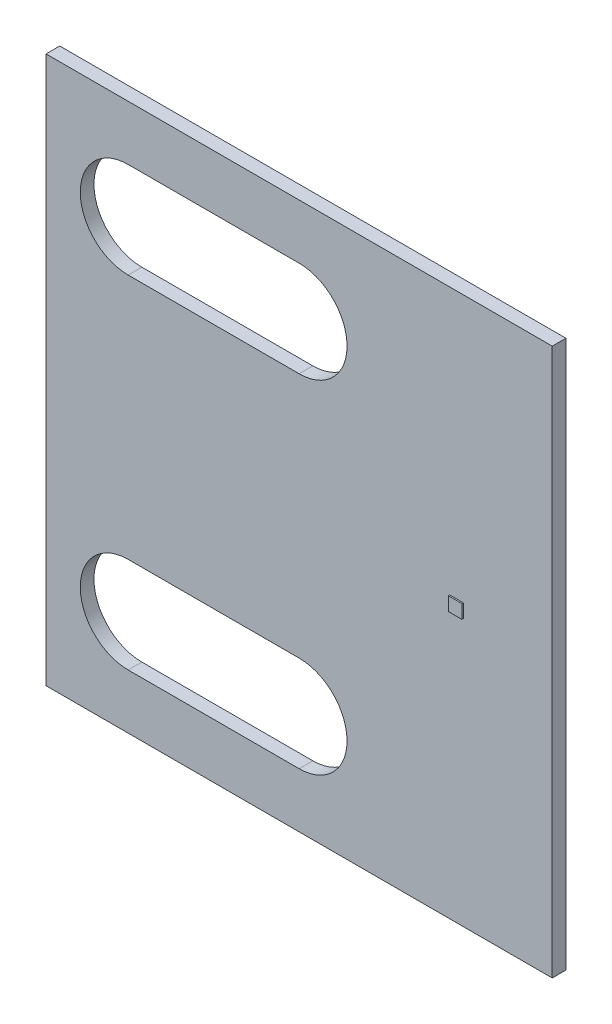
SolidWorks part; units mm, degrees
ref_plane "Front Plane" through (0, 0, 0) normal (0, 0, 1) x (1, 0, 0)
ref_plane "Top Plane" through (0, 0, 0) normal (0, 1, 0) x (1, 0, 0)
ref_plane "Right Plane" through (0, 0, 0) normal (1, 0, 0) x (0, 0, -1)
sketch "Sketch1" plane through (0, 0, 0) normal (0, 0, 1) x (1, 0, 0)
  line L1 (-30, 20) -> (7, 20)
  line L2 (-30, 20) -> (-30, -20)
  line L3 (-30, -20) -> (7, -20)
  line L4 (7, 20) -> (7, -20)
  line L5 (-30, 20) -> (7, -20) construction
  line L6 (-30, -20) -> (7, 20) construction
  point P0 (-11.5, 0)
  dimension "D1" = 37
  dimension "D2" = 40
  dimension "D3" = 20
  dimension "D4" = 7
extrude "Boss-Extrude1" add sketch "Sketch1" along normal blind 1
sketch "Sketch2" plane through (0, 0, 1) normal (0, 0, 1) x (1, 0, 0)
  line L1 (-0.5, -0.5) -> (0.5, -0.5)
  line L2 (-0.5, -0.5) -> (-0.5, 0.5)
  line L3 (-0.5, 0.5) -> (0.5, 0.5)
  line L4 (0.5, -0.5) -> (0.5, 0.5)
  line L5 (-0.5, -0.5) -> (0.5, 0.5) construction
  line L6 (-0.5, 0.5) -> (0.5, -0.5) construction
  point P0 (0, 0)
  dimension "D1" = 1
  dimension "D2" = 1
extrude "Boss-Extrude2" add sketch "Sketch2" along normal blind 0.1
sketch "Sketch3" plane through (0, 0, 1) normal (0, 0, 1) x (1, 0, 0)
  line L0 (7, 20) -> (-30, 20) construction
  line L1 (-24, 16) -> (-11.5, 16)
  line L3 (-24, 9) -> (-11.5, 9)
  line L5 (-24, 16) -> (-11.5, 9) construction
  line L6 (-24, 9) -> (-11.5, 16) construction
  arc A0 (-24, 16) -> (-24, 9) centre (-24, 12.5) ccw
  arc A1 (-11.5, 16) -> (-11.5, 9) centre (-11.5, 12.5) cw
  point P0 (-17.75, 12.5)
  dimension "D1" = 7.5
  dimension "D2" = 12.5
  dimension "D4" = 7
extrude "Cut-Extrude1" cut sketch "Sketch3" against normal through all
mirror "Mirror1" about plane through (0, 0, 0) normal (0, 1, 0) of "Cut-Extrude1"
